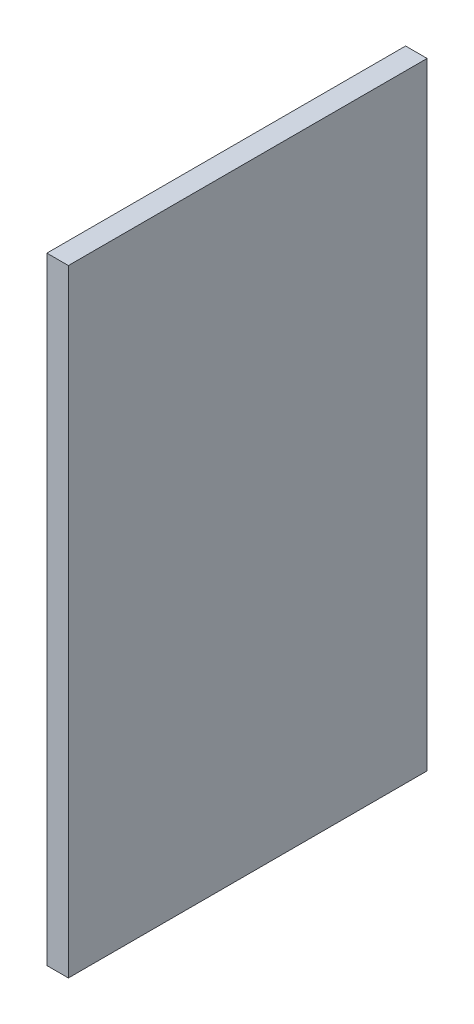
SolidWorks part; units mm, degrees
material "Aço carbono simples"
ref_plane "Plano frontal" through (0, 0, 0) normal (0, 0, 1) x (1, 0, 0)
ref_plane "Plano superior" through (0, 0, 0) normal (0, 1, 0) x (1, 0, 0)
ref_plane "Plano direito" through (0, 0, 0) normal (1, 0, 0) x (0, 0, -1)
sketch "Esboço1" plane through (0, 0, 0) normal (1, 0, 0) x (0, 0, -1)
  line L0 (125, -215) -> (-125, 215) construction
  line L1 (-125, 215) -> (125, 215)
  line L2 (-125, 215) -> (-125, -215)
  line L3 (-125, -215) -> (125, -215)
  line L4 (125, 215) -> (125, -215)
  line L5 (125, 215) -> (-125, -215) construction
  point P5 (0, 0)
  dimension "D1" = 250
  dimension "D2" = 430
extrude "Ressalto-extrusão1" add sketch "Esboço1" along normal blind 15
sketch "Esboço4" plane through (0, 0, 0) normal (-1, 0, 0) x (0, 0, 1)
  line L0 (-25, 0) -> (25, 0) construction
  line L1 (-25, 0) -> (25, 0)
  arc A0 (-25, 0) -> (25, 0) centre (0, 0) ccw
revolve "Revolução1" add sketch "Esboço4" angle 180 about L0
